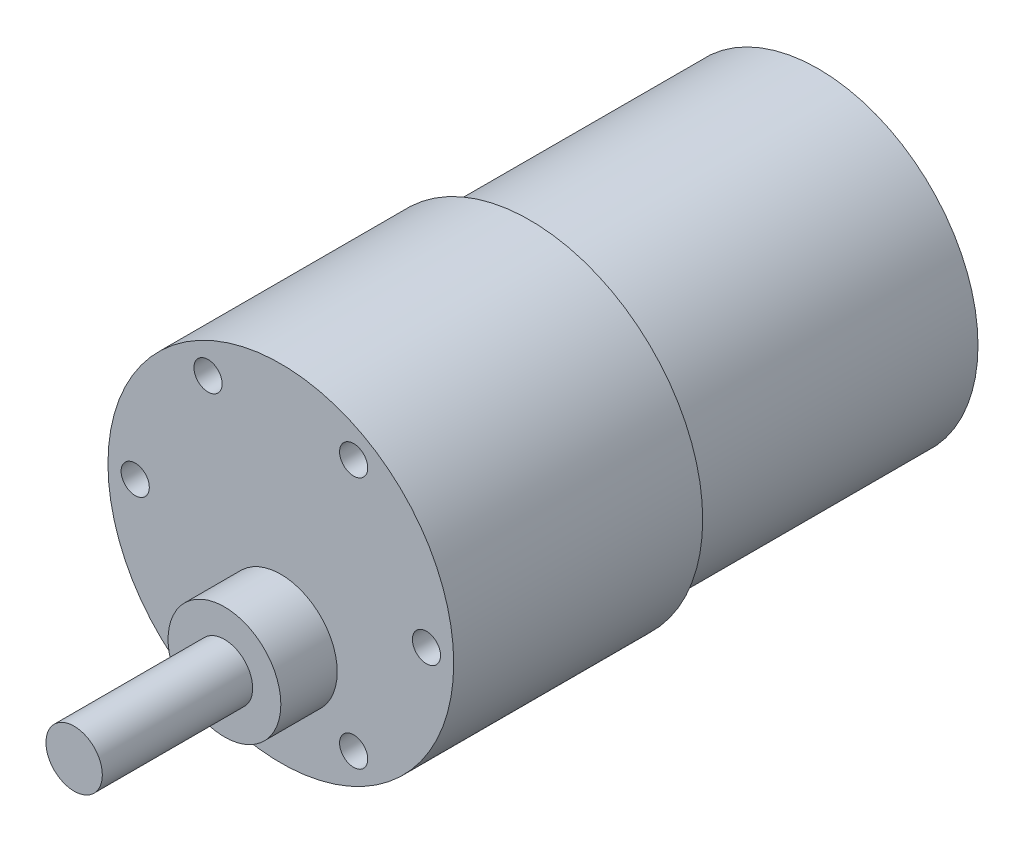
SolidWorks part; units mm, degrees
ref_plane "Alzado" through (0, 0, 0) normal (0, 0, 1) x (1, 0, 0)
ref_plane "Planta" through (0, 0, 0) normal (0, 1, 0) x (1, 0, 0)
ref_plane "Vista lateral" through (0, 0, 0) normal (1, 0, 0) x (0, 0, -1)
sketch "Croquis1" plane through (0, 0, 0) normal (0, 0, 1) x (1, 0, 0)
  circle A0 centre (0, 0) radius 18.4
  dimension "D1" = 36.8
extrude "Saliente-Extruir1" add sketch "Croquis1" along normal blind 26.5
sketch "Croquis2" plane through (0, 0, 0) normal (0, 0, -1) x (-1, 0, 0)
  circle A0 centre (0, 0) radius 17
  dimension "D1" = 34
extrude "Saliente-Extruir2" add sketch "Croquis2" along normal blind 30.7
sketch "Croquis3" plane through (0, 0, 26.5) normal (0, 0, 1) x (1, 0, 0)
  line L0 (-15.5, 0) -> (15.5, 0) construction
  circle A0 centre (0, 0) radius 15.5 construction
  circle A1 centre (-15.5, 0) radius 1.5
  circle A2 centre (-7.75, 13.4234) radius 1.5
  circle A3 centre (7.75, 13.4234) radius 1.5
  circle A4 centre (15.5, 0) radius 1.5
  circle A5 centre (7.75, -13.4234) radius 1.5
  circle A6 centre (-7.75, -13.4234) radius 1.5
  point P17 (0, 0)
  dimension "D3" = 3
  dimension "D2" = 15.5
  dimension "D1" = 6
extrude "Cortar-Extruir1" cut sketch "Croquis3" against normal blind 5
sketch "Croquis4" plane through (0, 0, 26.5) normal (0, 0, 1) x (1, 0, 0)
  line L0 (0, 0) -> (0, -7) construction
  line L1 (0, 0) -> (-18.4, 0) construction
  circle A0 centre (0, -7) radius 6
  circle A1 centre (0, 0) radius 18.4 construction
  dimension "D2" = 12
  dimension "D1" = 7
extrude "Saliente-Extruir3" add sketch "Croquis4" along normal blind 6
sketch "Croquis5" plane through (0, 0, 32.5) normal (0, 0, 1) x (1, 0, 0)
  circle A0 centre (0, -7) radius 3
  circle A2 centre (0, -7) radius 6 construction
  dimension "D1" = 6
extrude "Saliente-Extruir4" add sketch "Croquis5" along normal blind 16
sketch "Croquis6" plane through (0, 0, 26.5) normal (0, 0, 1) x (1, 0, 0)
  circle A0 centre (-7.75, 13.4234) radius 1.5 construction
  circle A1 centre (0, 0) radius 18.4
  circle A2 centre (0, 0) radius 18.4
  circle A3 centre (7.75, 13.4234) radius 1.5 construction
  circle A4 centre (15.5, 0) radius 1.5 construction
  circle A5 centre (7.75, -13.4234) radius 1.5 construction
  circle A6 centre (-7.75, -13.4234) radius 1.5 construction
  circle A7 centre (-15.5, 0) radius 1.5 construction
  circle A8 centre (0, -7) radius 3 construction
  circle A9 centre (0, -7) radius 6 construction
  circle A10 centre (-7.75, 13.4234) radius 1.5
  circle A11 centre (7.75, 13.4234) radius 1.5
  circle A12 centre (15.5, 0) radius 1.5
  circle A13 centre (7.75, -13.4234) radius 1.5
  circle A14 centre (-7.75, -13.4234) radius 1.5
  circle A15 centre (-15.5, 0) radius 1.5
  circle A16 centre (0, -7) radius 3
  circle A17 centre (0, -7) radius 6
  dimension "D1" = 0
